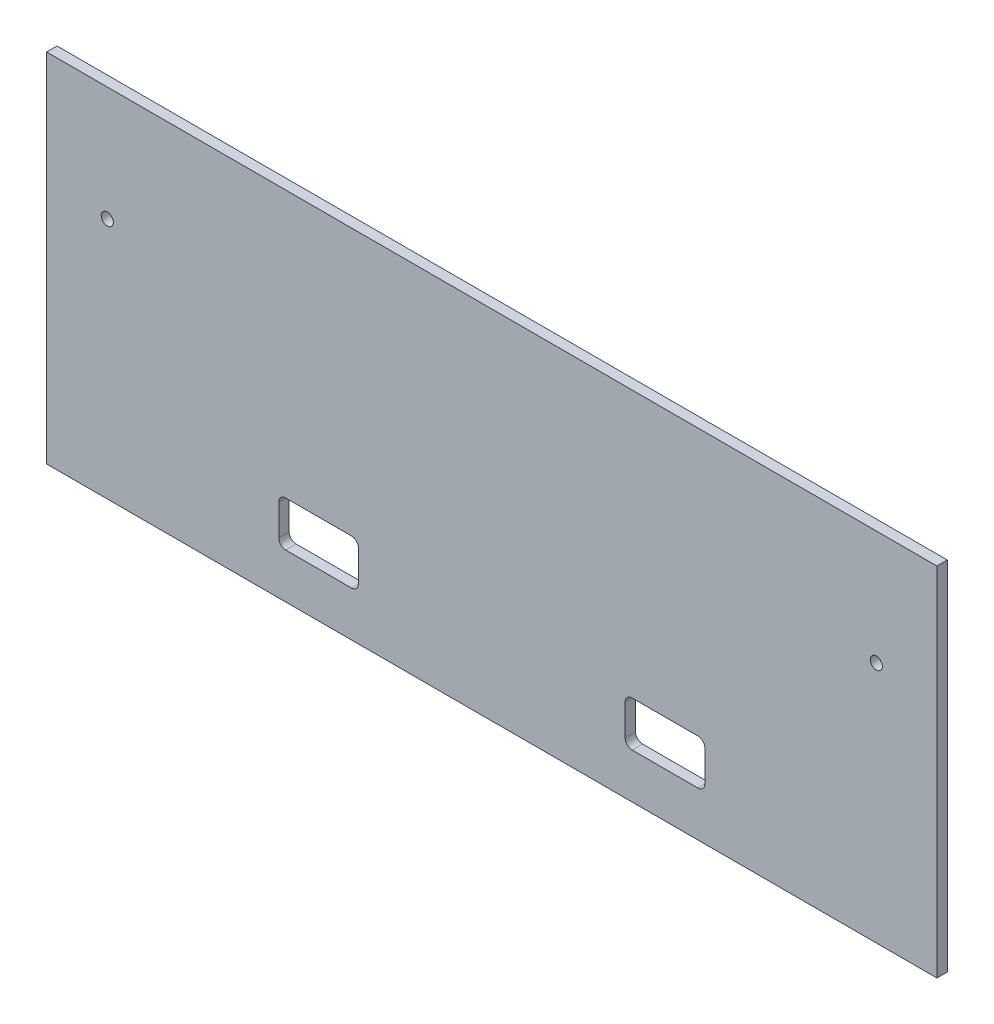
SolidWorks part; units mm, degrees
ref_plane "Plan de face" through (0, 0, 0) normal (0, 0, 1) x (1, 0, 0)
ref_plane "Plan de dessus" through (0, 0, 0) normal (0, 1, 0) x (1, 0, 0)
ref_plane "Plan de droite" through (0, 0, 0) normal (1, 0, 0) x (0, 0, -1)
sketch "Esquisse1" plane through (0, 0, 0) normal (0, 0, 1) x (1, 0, 0)
  line L0 (0, 51.5) -> (0, -51.5) construction
  line L1 (128.5, 51.5) -> (-128.5, 51.5)
  line L2 (128.5, 51.5) -> (128.5, -51.5)
  line L3 (128.5, -51.5) -> (-128.5, -51.5)
  line L4 (-128.5, 51.5) -> (-128.5, -51.5)
  line L5 (128.5, 51.5) -> (-128.5, -51.5) construction
  line L6 (128.5, -51.5) -> (-128.5, 51.5) construction
  line L7 (-111, 18.5) -> (0, 18.5) construction
  circle A0 centre (-111, 18.5) radius 1.75
  circle A1 centre (111, 18.5) radius 1.75
  point P0 (0, 0)
  dimension "D3" = 3.5
  dimension "D1" = 257
  dimension "D2" = 103
  dimension "D4" = 111
  dimension "D5" = 33
extrude "Boss.-Extru.1" add sketch "Esquisse1" along normal blind 3
sketch "Esquisse2" plane through (0, 0, 3) normal (0, 0, 1) x (1, 0, 0)
  line L0 (-38.5, -38.5) -> (38.5, -38.5) construction
  line L1 (-61.5, -38.5) -> (-38.5, -38.5)
  line L2 (-61.5, -38.5) -> (-61.5, -25.5)
  line L3 (-61.5, -25.5) -> (-38.5, -25.5)
  line L4 (-38.5, -38.5) -> (-38.5, -25.5)
  line L5 (38.5, -38.5) -> (61.5, -38.5)
  line L6 (38.5, -38.5) -> (38.5, -25.5)
  line L7 (38.5, -25.5) -> (61.5, -25.5)
  line L8 (61.5, -38.5) -> (61.5, -25.5)
  line L9 (0, 0) -> (0, -38.5) construction
  line L10 (-128.5, -51.5) -> (128.5, -51.5) construction
  point P8 (-50, -25.5)
  point P9 (50, -25.5)
  dimension "D1" = 100
  dimension "D2" = 23
  dimension "D3" = 13
  dimension "D4" = 13
extrude "Enlèv. mat.-Extru.1" cut sketch "Esquisse2" against normal up to next
fillet "Congé1" radius 2 8 edges at (38.5, -38.5, 1.5) (61.5, -38.5, 1.5) (61.5, -25.5, 1.5) (38.5, -25.5, 1.5) (-61.5, -38.5, 1.5) (-38.5, -38.5, 1.5) (-38.5, -25.5, 1.5) (-61.5, -25.5, 1.5)
